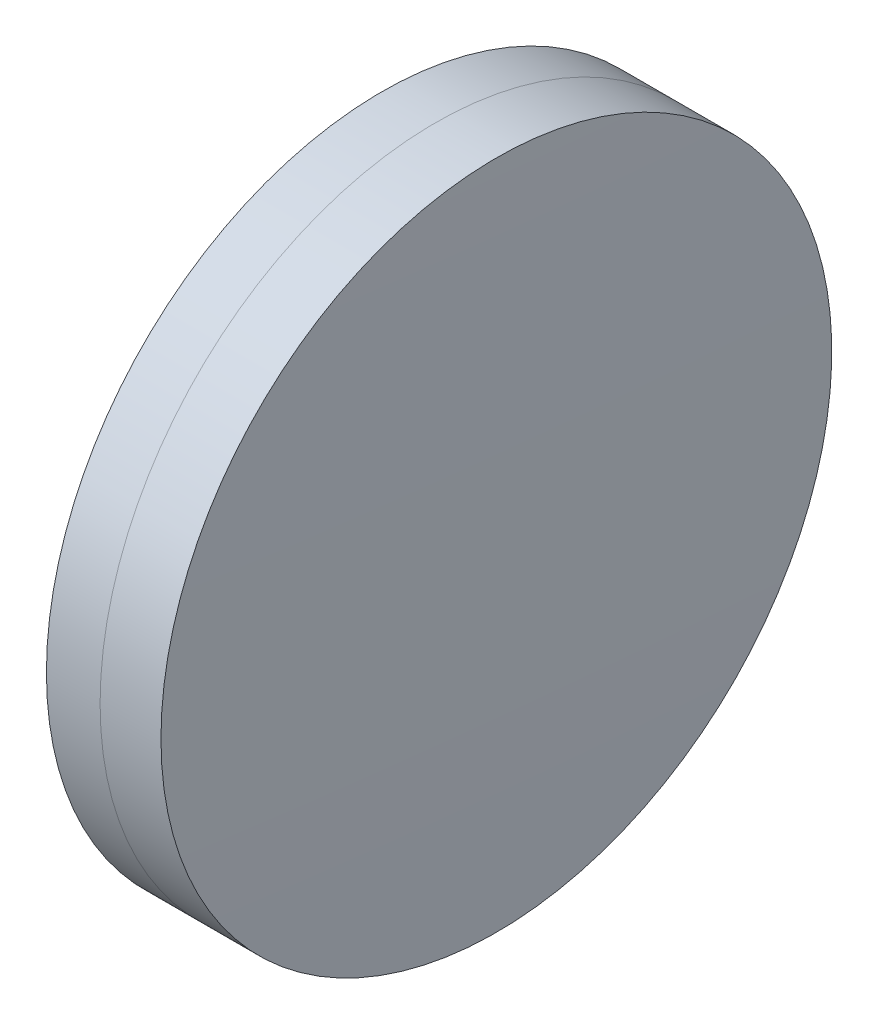
SolidWorks part; units mm, degrees
ref_plane "前视基准面" through (0, 0, 0) normal (0, 0, 1) x (1, 0, 0)
ref_plane "上视基准面" through (0, 0, 0) normal (0, 1, 0) x (1, 0, 0)
ref_plane "右视基准面" through (0, 0, 0) normal (1, 0, 0) x (0, 0, -1)
sketch "草图1" plane through (0, 0, 0) normal (0, 1, 0) x (1, 0, 0)
  line L0 (-9.7026, 0) -> (238.8542, 0) construction
  line L1 (215.4943, -12.5) -> (217.4945, -12.5)
  line L2 (215.4943, 12.5) -> (217.4945, 12.5)
  arc A0 (217.4945, -12.5) -> (217.4945, 12.5) centre (14.8797, 0) ccw
  arc A1 (215.4943, 12.5) -> (215.4943, -12.5) centre (522.2397, 0) ccw
  point P4 (233.0818, 0)
  point P6 (238.8542, 0)
  point P10 (215.2397, 0)
  point P11 (217.8797, 0)
  dimension "D3" = 307
  dimension "D4" = 203
  dimension "D1" = 12.5
  dimension "D2" = 12.5
  dimension "D5" = 2.64
revolve "旋转1" add sketch "草图1" angle 360 about L0
sketch "草图2" plane through (0, 0, 0) normal (0, 1, 0) x (1, 0, 0)
  line L0 (-0.5519, 0) -> (253.9868, 0) construction
  line L2 (217.4945, 12.5) -> (219.763, 12.5)
  line L3 (217.4945, -12.5) -> (219.763, -12.5)
  arc A0 (219.763, -12.5) -> (219.763, 12.5) centre (-449.9203, 0) ccw
  arc A1 (217.4945, -12.5) -> (217.4945, 12.5) centre (14.8797, 0) ccw construction
  arc A2 (217.4945, -12.5) -> (217.4945, 12.5) centre (14.8797, 0) ccw
  point P4 (217.8797, 0)
  point P8 (219.8797, 0)
  point P9 (253.9868, 0)
  dimension "D1" = 669.8
  dimension "D2" = 2
revolve "旋转3" add sketch "草图2" angle 360 about L0
